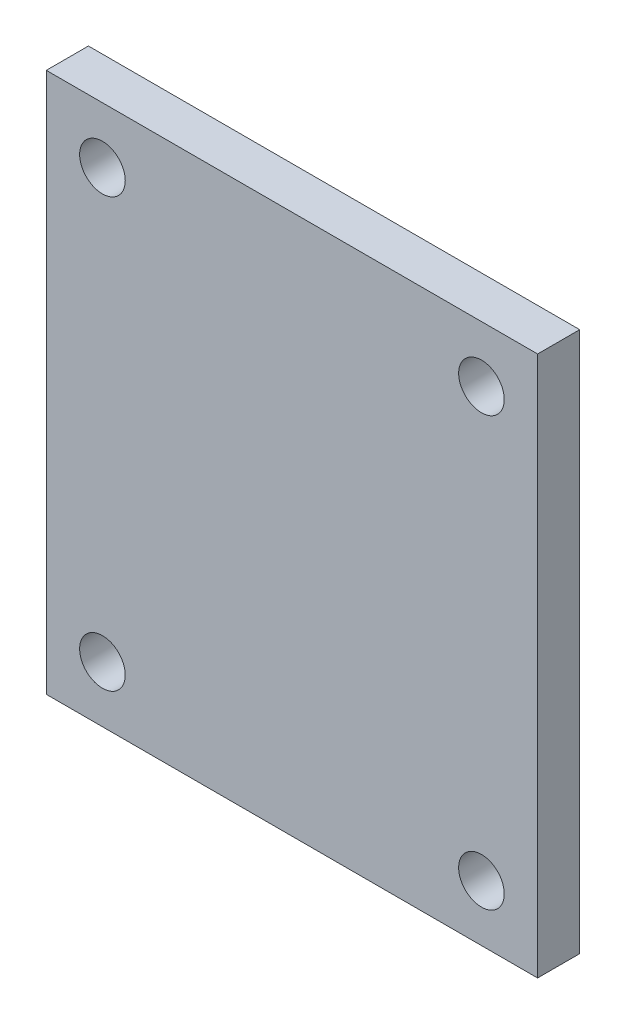
SolidWorks part; units mm, degrees
material "Plain Carbon Steel"
ref_plane "Front Plane" through (0, 0, 0) normal (0, 0, 1) x (1, 0, 0)
ref_plane "Top Plane" through (0, 0, 0) normal (0, 1, 0) x (1, 0, 0)
ref_plane "Right Plane" through (0, 0, 0) normal (1, 0, 0) x (0, 0, -1)
sketch "Sketch1" plane through (0, 0, 0) normal (0, 0, 1) x (1, 0, 0)
  line L0 (-70, -77) -> (70, -77)
  line L1 (-70, -77) -> (-70, 77)
  line L2 (70, -77) -> (70, 77)
  line L3 (-70, 77) -> (70, 77)
  line L4 (-70, -77) -> (70, 77) construction
  line L5 (70, -77) -> (-70, 77) construction
  line L6 (-70, 0) -> (70, 0) construction
  line L7 (0, 77) -> (0, -77) construction
  circle A0 centre (-54, 61) radius 6.5
  circle A1 centre (54, 61) radius 6.5
  circle A2 centre (-54, -61) radius 6.5
  circle A3 centre (54, -61) radius 6.5
  point P1 (0, 0)
  dimension "D3" = 13
  dimension "D5" = 16
  dimension "D1" = 140
  dimension "D2" = 16
  dimension "D4" = 154
extrude "Boss-Extrude1" add sketch "Sketch1" along normal mid plane 12
